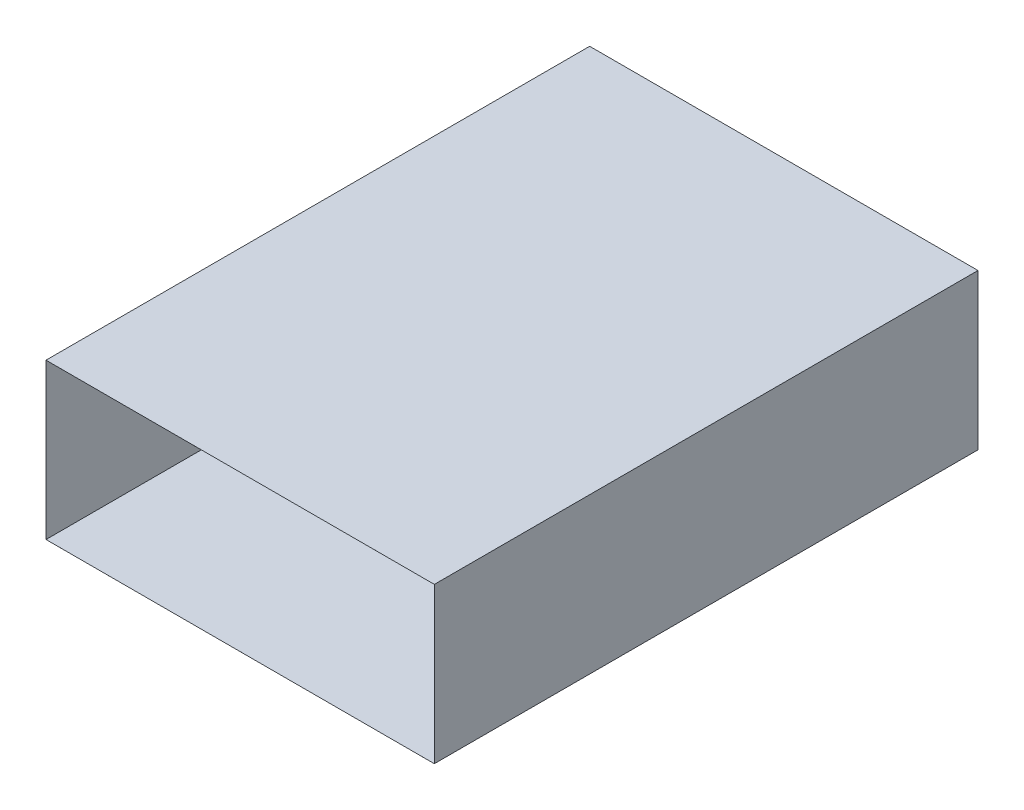
SolidWorks part; units mm, degrees
ref_plane "Plan de face" through (0, 0, 0) normal (0, 0, 1) x (1, 0, 0)
ref_plane "Plan de dessus" through (0, 0, 0) normal (0, 1, 0) x (1, 0, 0)
ref_plane "Plan de droite" through (0, 0, 0) normal (1, 0, 0) x (0, 0, -1)
sketch "Esquisse1" plane through (0, 0, 0) normal (0, 0, 1) x (1, 0, 0)
  line L1 (-125, -50) -> (125, -50)
  line L2 (-125, -50) -> (-125, 50)
  line L3 (-125, 50) -> (125, 50)
  line L4 (125, -50) -> (125, 50)
  line L5 (-125, -50) -> (125, 50) construction
  line L6 (-125, 50) -> (125, -50) construction
  point P0 (0, 0)
  dimension "D1" = 250
  dimension "D2" = 100
extrude "Extru.-Mince1" add sketch "Esquisse1" along normal blind 350 thin
